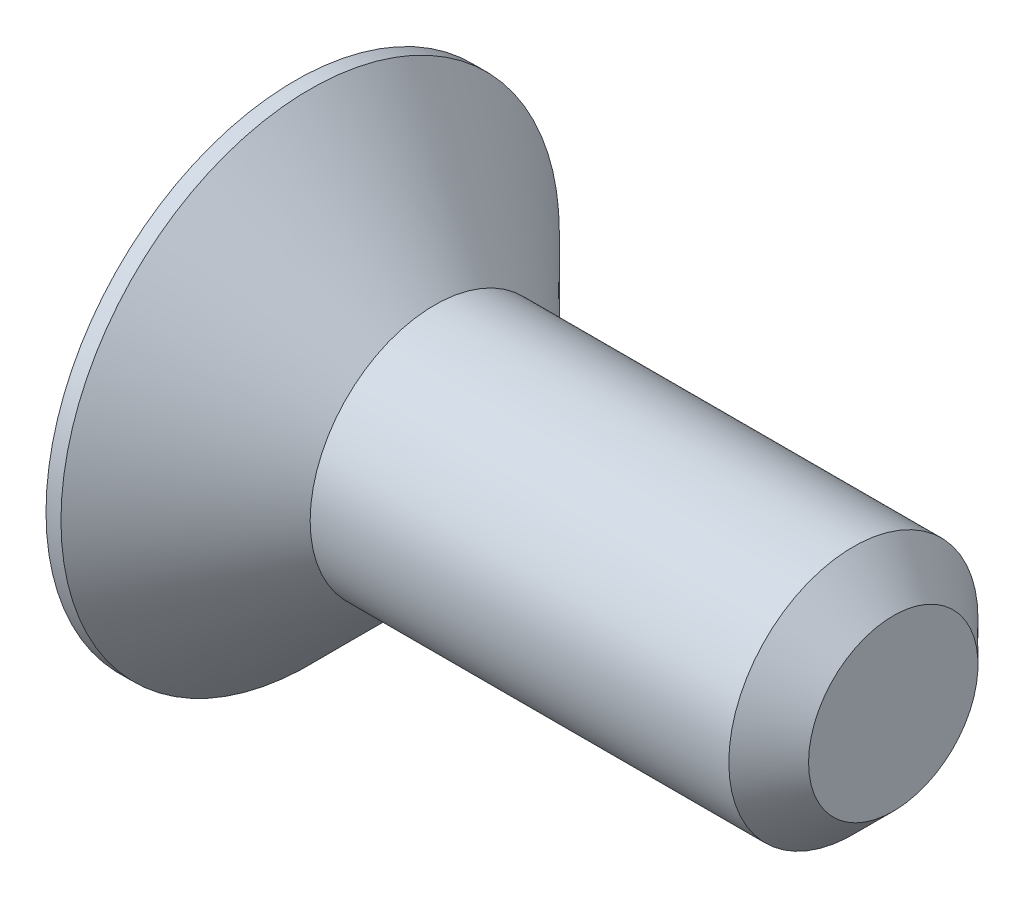
SolidWorks part; units mm, degrees
ref_plane "Front Plane" through (0, 0, 0) normal (0, 0, 1) x (1, 0, 0)
ref_plane "Top Plane" through (0, 0, 0) normal (0, 1, 0) x (1, 0, 0)
ref_plane "Right Plane" through (0, 0, 0) normal (1, 0, 0) x (0, 0, -1)
sketch "Sketch1" plane through (0, 0, 0) normal (0, 0, 1) x (1, 0, 0)
  line L0 (-2.8, 0) -> (9.2, 0) construction
  line L2 (0, -2.5) -> (8.4, -2.5)
  line L4 (-2.8, -5) -> (-2.5, -5)
  line L5 (9.2, -1.7) -> (9.2, 0)
  line L6 (-2.8, -5) -> (-2.8, 0)
  line L7 (-2.8, 0) -> (9.2, 0)
  line L9 (-2.5, -5) -> (0, -2.5)
  line L11 (8.4, -2.5) -> (9.2, -1.7)
  line L12 (9.2, 1.7) -> (8.4, 2.5) construction
  point P8 (-2.8, -5.6)
  point P12 (-2.8, 5.6)
  point P13 (8.4, -2.5)
  point P14 (-2.8, 5)
  dimension "L" = 12
  dimension "FIX_1" = 45
  dimension "M" = 5
  dimension "Pitch" = 0.8
  dimension "BLT_3" = 0.8
  dimension "FIX_2" = 45
  dimension "BLT_1" = 11.2
  dimension "E" = 2.8
  dimension "A" = 10
revolve "Revolve1" add sketch "Sketch1" angle 360 about L0
cosmetic thread "Thread1"
sketch "Sketch2" plane through (-2.8, 0, 0) normal (-1, 0, 0) x (0, 0, 1)
  line L1 (0, 1.7321) -> (-1.5, 0.866)
  line L2 (-1.5, 0.866) -> (-1.5, -0.866)
  line L3 (-1.5, -0.866) -> (0, -1.7321)
  line L4 (0, -1.7321) -> (1.5, -0.866)
  line L5 (1.5, -0.866) -> (1.5, 0.866)
  line L6 (1.5, 0.866) -> (0, 1.7321)
  circle A0 centre (0, 0) radius 1.5 construction
  dimension "B" = 3
extrude "Cut-Extrude1" cut sketch "Sketch2" against normal blind 1.9
equation "\"Pitch\"= iif ( \"M\" = 10 , 1.5 , iif ( \"M\" = 8 , 1.25 , iif ( \"M\" = 6 , 1 , iif ( \"M\" = 5 , 0.8 , iif ( \"M\" = 4 , 0.7 , iif ( \"M\" = 3 , 0.5 , iif ( \"M\" = 2.5 , 0.45 , 0.4 ) ) ) ) ) ) )"
equation "\"Factor\"= 1.082532"
equation "\"ATD_1\"= round ( \"M\" - \"Factor\" * \"Pitch\" , 3 )"
equation "\"BLT_3@Sketch1\"= \"Pitch\""
